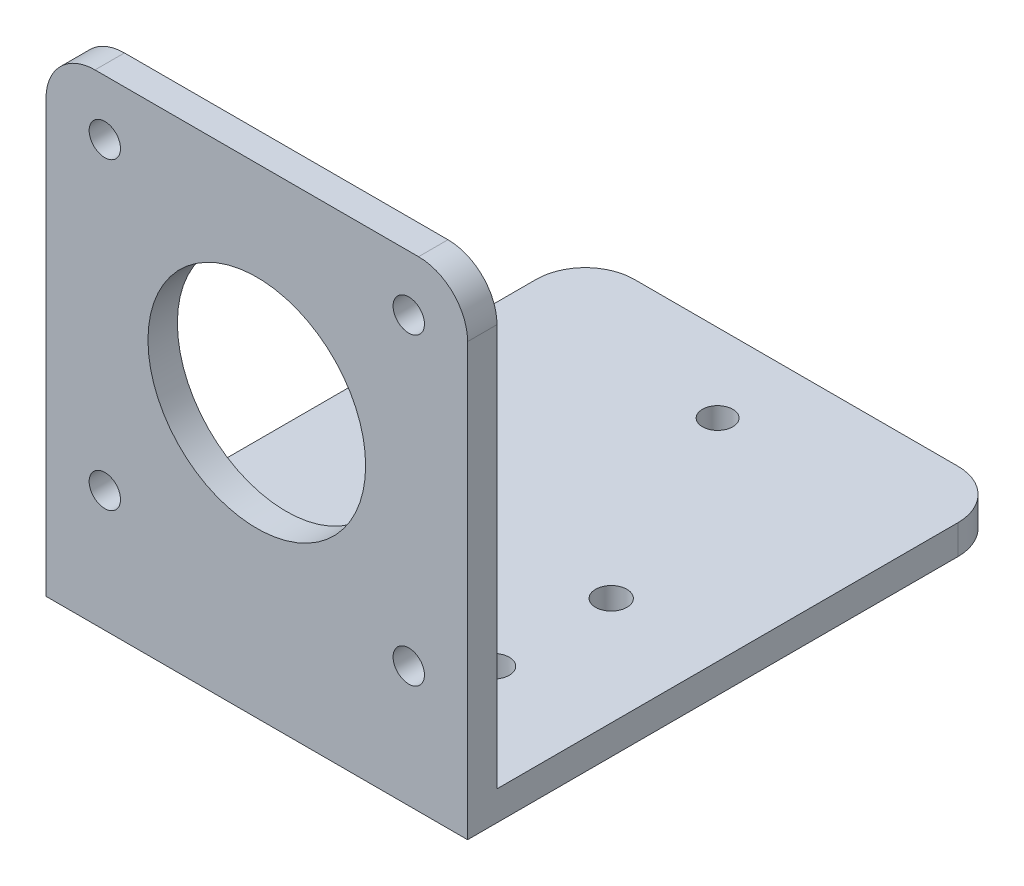
SolidWorks part; units mm, degrees
ref_plane "前视基准面" through (0, 0, 0) normal (0, 0, 1) x (1, 0, 0)
ref_plane "上视基准面" through (0, 0, 0) normal (0, 1, 0) x (1, 0, 0)
ref_plane "右视基准面" through (0, 0, 0) normal (1, 0, 0) x (0, 0, -1)
sketch "草图3" plane through (0, 0, 0) normal (0, 0, 1) x (1, 0, 0)
  line L1 (0, 0) -> (43, 0)
  line L2 (0, 0) -> (0, -49)
  line L3 (0, -49) -> (43, -49)
  line L4 (43, 0) -> (43, -49)
  dimension "D1" = 43
  dimension "D2" = 49
extrude "凸台-拉伸2" add sketch "草图3" along normal blind 3
sketch "草图6" plane through (0, 0, 0) normal (0, 0, -1) x (-1, 0, 0)
  line L0 (-43, -46) -> (0, -46) construction
  line L1 (-43, -49) -> (-43, 0) construction
  line L2 (0, 0) -> (0, -49) construction
  line L3 (-43, 0) -> (0, 0) construction
  line L5 (-21.5, -21.15) -> (-56.0988, -21.15) construction
  line L6 (-21.5, -21.15) -> (-21.5, 3.3145) construction
  circle A1 centre (-21.5, -21.15) radius 11.1
  circle A5 centre (-37, -5.65) radius 1.6
  circle A6 centre (-6, -5.65) radius 1.6
  circle A7 centre (-6, -36.65) radius 1.6
  circle A8 centre (-37, -36.65) radius 1.6
  dimension "D2" = 22.2
  dimension "D3" = 3.2
  dimension "D1" = 3
  dimension "D4" = 31
  dimension "D5" = 31
  dimension "D6" = 21.15
extrude "切除-拉伸2" cut sketch "草图6" against normal blind 45
sketch "草图7" plane through (0, 0, 0) normal (0, 0, -1) x (-1, 0, 0)
  line L0 (0, 0) -> (0, -49) construction
  line L1 (-43, -49) -> (0, -49)
  line L2 (-43, -49) -> (-43, -46)
  line L3 (-43, -46) -> (0, -46)
  line L4 (0, -49) -> (0, -46)
  dimension "D1" = 3
extrude "凸台-拉伸4" add sketch "草图7" along normal blind 52
sketch "草图8" plane through (0, -46, 0) normal (0, 1, 0) x (1, 0, 0)
  line L0 (0, 52) -> (43, 0) construction
  line L1 (43, 52) -> (0, 0) construction
  line L2 (21.5, 26) -> (21.5, -8.6818) construction
  line L3 (0, 0) -> (43, 0) construction
  line L4 (11, 22.65) -> (11, 10.65) construction
  line L5 (21.5, 44) -> (21.5, 26) construction
  line L6 (0, 52) -> (43, 52) construction
  circle A0 centre (11, 10.65) radius 1.6
  circle A1 centre (11, 22.65) radius 1.6
  circle A2 centre (32, 10.65) radius 1.6
  circle A3 centre (32, 22.65) radius 1.6
  circle A4 centre (21.5, 44) radius 1.55
  dimension "D1" = 3.2
  dimension "D3" = 3.2
  dimension "D6" = 3.1
  dimension "D2" = 10.65
  dimension "D4" = 21
  dimension "D5" = 12
  dimension "D7" = 8
extrude "切除-拉伸3" cut sketch "草图8" against normal blind 45
fillet "圆角1" radius 5 4 edges at (43, -47.5, -52) (0, -47.5, -52) (0, 0, 1.5) (43, 0, 1.5)
